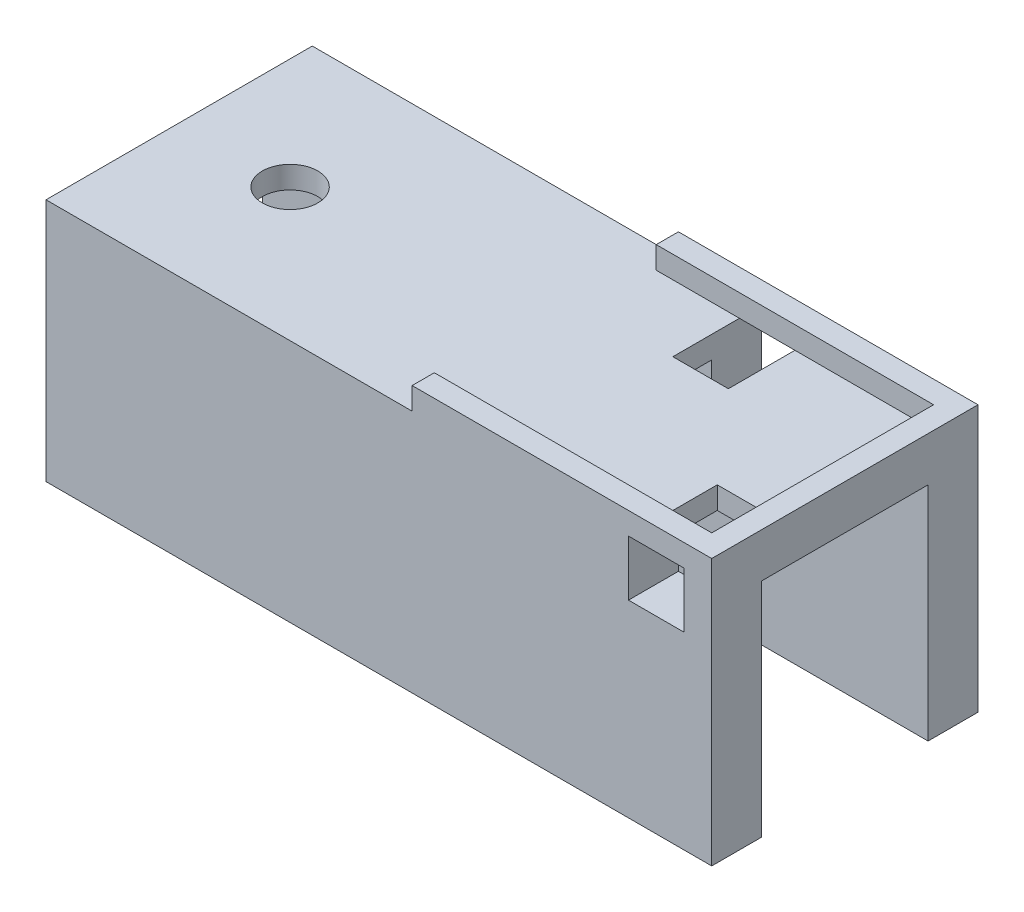
SolidWorks part; units mm, degrees
ref_plane "Plan de face" through (0, 0, 0) normal (0, 0, 1) x (1, 0, 0)
ref_plane "Plan de dessus" through (0, 0, 0) normal (0, 1, 0) x (1, 0, 0)
ref_plane "Plan de droite" through (0, 0, 0) normal (1, 0, 0) x (0, 0, -1)
sketch "Esquisse1" plane through (0, 0, 0) normal (0, 1, 0) x (1, 0, 0)
  line L0 (0, 0) -> (60, 0) construction
  line L2 (0, 12) -> (60, 12)
  line L3 (0, 12) -> (0, -12)
  line L4 (0, -12) -> (60, -12)
  line L5 (60, 12) -> (60, -12)
  circle A0 centre (10, 0) radius 2.5
  point P9 (60.7923, 0)
  dimension "D2" = 50
  dimension "D3" = 5
  dimension "D1" = 60
  dimension "D4" = 24
extrude "Boss.-Extru.1" add sketch "Esquisse1" along normal blind 2
sketch "Esquisse2" plane through (0, 2, 0) normal (0, 1, 0) x (1, 0, 0)
  line L0 (33, 12) -> (33, -12)
  line L1 (60, 12) -> (0, 12) construction
  line L2 (0, -12) -> (60, -12) construction
  line L12 (2, 10) -> (2, -10)
  line L13 (2, -10) -> (58, -10)
  line L14 (58, -10) -> (58, 10)
  line L15 (58, 10) -> (2, 10)
  line L16 (2, 10) -> (2, -10)
  line L17 (2, -10) -> (58, -10)
  line L18 (58, -10) -> (58, 10)
  line L19 (58, 10) -> (2, 10)
  line M7 (0, -12) -> (60, -12)
  line M8 (60, -12) -> (60, 12)
  line M9 (60, 12) -> (0, 12)
  dimension "D2" = 25
  dimension "D1" = 2
extrude "Boss.-Extru.2" add sketch "Esquisse2" along normal blind 2 contours L19 L18 L17 L0 M7 M8 M9
sketch "Esquisse3" plane through (0, 0, 0) normal (0, -1, 0) x (1, 0, 0)
  line L0 (0, 0) -> (60, 0) construction
  line L1 (0, 7.5) -> (60, 7.5)
  line L2 (0, -7.5) -> (60, -7.5)
  line L4 (0, 12) -> (0, -12)
  line L5 (0, -12) -> (60, -12)
  line L6 (60, -12) -> (60, 12)
  line L7 (60, 12) -> (0, 12)
  line L8 (0, 12) -> (0, -12)
  line L9 (0, -12) -> (60, -12)
  line L10 (60, -12) -> (60, 12)
  line L11 (60, 12) -> (0, 12)
  line M8 (0, 12) -> (0, -12)
  line M9 (0, -12) -> (60, -12)
  line M10 (60, -12) -> (60, 12)
  line M11 (60, 12) -> (0, 12)
  dimension "D2" = 15
  dimension "D1" = 0
extrude "Boss.-Extru.3" add sketch "Esquisse3" along normal blind 20 contours L1 M8 M10 M11 | L2 M8 M9 M10
sketch "Esquisse5" plane through (0, 0, 12) normal (0, 0, 1) x (1, 0, 0)
  line L0 (33, 2) -> (60, 2) construction
  line L2 (57.5, 2) -> (52.5, 2)
  line L3 (57.5, 2) -> (57.5, -3)
  line L4 (57.5, -3) -> (52.5, -3)
  line L5 (52.5, 2) -> (52.5, -3)
  line L6 (0, 2) -> (0, -20)
  line L7 (0, -20) -> (60, -20)
  line L8 (60, -20) -> (60, 4)
  line L9 (60, 4) -> (33, 4)
  line L10 (33, 4) -> (33, 2)
  line L11 (33, 2) -> (0, 2)
  line L12 (0, 2) -> (0, -20)
  line L13 (0, -20) -> (60, -20)
  line L14 (60, -20) -> (60, 4)
  line L15 (60, 4) -> (33, 4)
  line L16 (33, 4) -> (33, 2)
  line L17 (33, 2) -> (0, 2)
  dimension "D2" = 2.5
  dimension "D3" = 5
  dimension "D4" = 5
  dimension "D1" = 0
extrude "Enlèv. mat.-Extru.2" cut sketch "Esquisse5" against normal blind 8 contours L2 L5 L4 L3
sketch "Esquisse6" plane through (0, 0, -12) normal (0, 0, -1) x (-1, 0, 0)
  line L0 (-33, 2) -> (-60, 2) construction
  line L2 (-45.5, 2) -> (-40.5, 2)
  line L3 (-45.5, 2) -> (-45.5, -3)
  line L4 (-45.5, -3) -> (-40.5, -3)
  line L5 (-40.5, 2) -> (-40.5, -3)
  line L6 (-60, 4) -> (-60, -20)
  line L7 (-60, -20) -> (0, -20)
  line L8 (0, -20) -> (0, 2)
  line L9 (0, 2) -> (-33, 2)
  line L10 (-33, 2) -> (-33, 4)
  line L11 (-33, 4) -> (-60, 4)
  line L12 (-60, 4) -> (-60, -20)
  line L13 (-60, -20) -> (0, -20)
  line L14 (0, -20) -> (0, 2)
  line L15 (0, 2) -> (-33, 2)
  line L16 (-33, 2) -> (-33, 4)
  line L17 (-33, 4) -> (-60, 4)
  dimension "D2" = 14.5
  dimension "D3" = 5
  dimension "D4" = 5
  dimension "D1" = 0
extrude "Enlèv. mat.-Extru.3" cut sketch "Esquisse6" against normal blind 8 contours L5 L2 L3 L4
